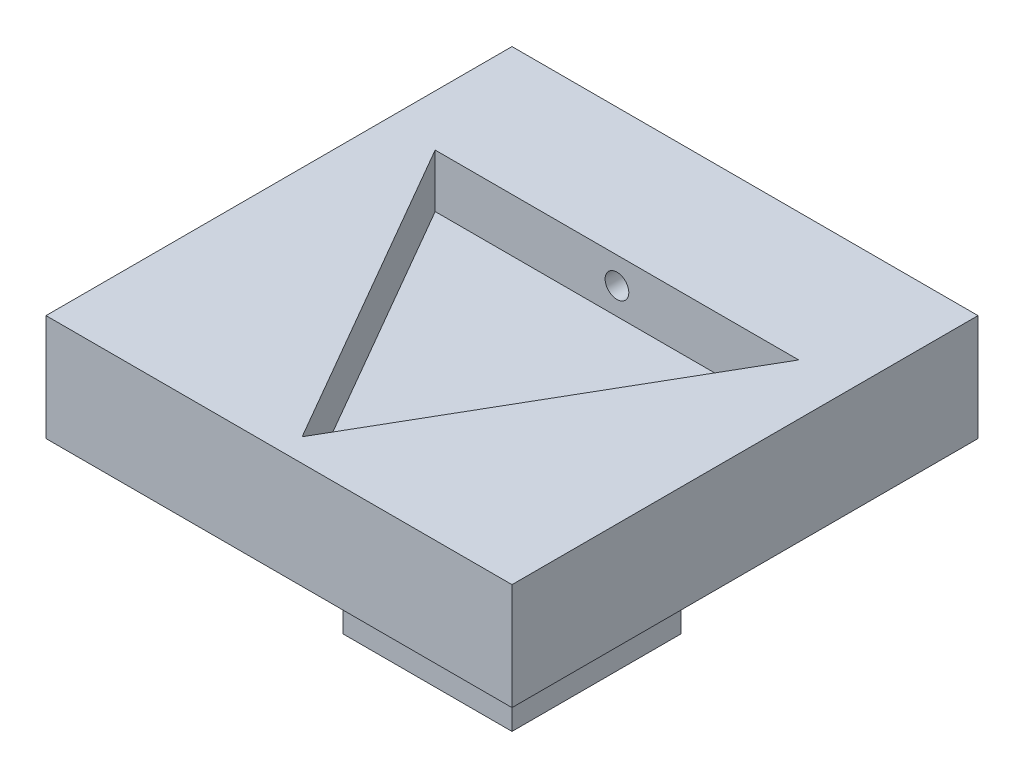
SolidWorks part; units mm, degrees
ref_plane "Front" through (0, 0, 0) normal (0, 0, 1) x (1, 0, 0)
ref_plane "Top" through (0, 0, 0) normal (0, 1, 0) x (1, 0, 0)
ref_plane "Right" through (0, 0, 0) normal (1, 0, 0) x (0, 0, -1)
sketch "Sketch1" plane through (0, 0, 0) normal (0, 1, 0) x (1, 0, 0)
  line L1 (-17.5, -17.5) -> (17.5, -17.5)
  line L2 (-17.5, -17.5) -> (-17.5, 17.5)
  line L3 (-17.5, 17.5) -> (17.5, 17.5)
  line L4 (17.5, -17.5) -> (17.5, 17.5)
  line L5 (-17.5, -17.5) -> (17.5, 17.5) construction
  line L6 (-17.5, 17.5) -> (17.5, -17.5) construction
  point P0 (0, 0)
  dimension "D1" = 35
  dimension "D2" = 35
extrude "Extrude1" add sketch "Sketch1" along normal blind 8
sketch "Sketch2" plane through (0, 8, 0) normal (0, 1, 0) x (1, 0, 0)
  line L0 (17.5, 17.5) -> (-17.5, 17.5) construction
  line L1 (0, -15.764) -> (13.652, 7.882)
  line L2 (13.652, 7.882) -> (-13.652, 7.882)
  line L3 (-13.652, 7.882) -> (0, -15.764)
  circle A0 centre (0, 0) radius 7.882 construction
  dimension "D1" = 23.646
  dimension "D2" = 17.5
extrude "Extrude2" cut sketch "Sketch2" against normal blind 4
sketch "Sketch3" plane through (0, 0, -17.5) normal (0, 0, -1) x (-1, 0, 0)
  line L0 (0, -15.1983) -> (0, 14.4979) construction
hole_wizard "#2-56 Tapped Hole1" positions "3DSketch1" profile "Sketch5" tap size "#2-56" standard "Ansi Inch" end condition up to next
sketch3d "3DSketch1"
  line L0 (0, -15.1983, -17.5) -> (0, 14.4979, -17.5) construction
  line L1 (17.5, 8, -17.5) -> (-17.5, 8, -17.5) construction
  point P0 (0, 6, -17.5)
  dimension "D1" = 2
sketch "Sketch5" plane through (0, 6, -17.5) normal (1, 0, 0) x (0, 1, 0)
  line L0 (0, 0) -> (0, 9.618)
  line L1 (0, 9.618) -> (0.889, 9.618)
  line L2 (0.889, 9.618) -> (0.889, 0)
  line L5 (0.889, 0) -> (0, 0)
  line L11 (0, -6.35) -> (0, 107.95) construction
  dimension "Thread Major Dia." = 1.778
  dimension "Thru Tap Drill Depth" = 9.618
sketch "Sketch6" plane through (0, 0, 0) normal (0, -1, 0) x (1, 0, 0)
  line L1 (-6.35, -6.35) -> (6.35, -6.35)
  line L2 (-6.35, -6.35) -> (-6.35, 6.35)
  line L3 (-6.35, 6.35) -> (6.35, 6.35)
  line L4 (6.35, -6.35) -> (6.35, 6.35)
  line L5 (-6.35, -6.35) -> (6.35, 6.35) construction
  line L6 (-6.35, 6.35) -> (6.35, -6.35) construction
  point P0 (0, 0)
  dimension "D1" = 12.7
  dimension "D2" = 12.7
extrude "Extrude3" add sketch "Sketch6" along normal blind 12.7
sketch "Sketch7" plane through (6.35, 0, 0) normal (1, 0, 0) x (0, 0, -1)
  line L0 (0, -16.8508) -> (0, 11.4455) construction
sketch "Sketch8" plane through (0, 0, 6.35) normal (0, 0, 1) x (1, 0, 0)
  line L0 (0, -17.0804) -> (0, 11.7392) construction
hole_wizard "1/4 (0.25) Diameter Hole1" positions "3DSketch2" profile "Sketch9" hole size "1/4" standard "Ansi Inch" end condition through all
sketch3d "3DSketch2"
  line L0 (0, -17.0804, 6.35) -> (0, 11.7392, 6.35) construction
  line L1 (6.35, -12.7, 6.35) -> (-6.35, -12.7, 6.35) construction
  point P0 (0, -6.35, 6.35)
  dimension "D1" = 6.35
sketch "Sketch9" plane through (0, -6.35, 6.35) normal (1, 0, 0) x (0, -1, 0)
  line L0 (0, 0) -> (0, 23.85)
  line L1 (0, 23.85) -> (3.175, 23.85)
  line L2 (3.175, 23.85) -> (3.175, 0)
  line L5 (3.175, 0) -> (0, 0)
  line L11 (0, -6.35) -> (0, 107.95) construction
  dimension "Thru Hole Dia." = 6.35
  dimension "Thru Hole Depth" = 23.85
hole_wizard "1/4 (0.25) Diameter Hole2" positions "3DSketch3" profile "Sketch10" hole size "1/4" standard "Ansi Inch" end condition through all
sketch3d "3DSketch3"
  line L0 (6.35, -16.8508, 0) -> (6.35, 11.4455, 0) construction
  line L1 (6.35, -12.7, -6.35) -> (6.35, -12.7, 6.35) construction
  point P0 (6.35, -6.35, 0)
  dimension "D1" = 6.35
sketch "Sketch10" plane through (6.35, -6.35, 0) normal (0, 1, 0) x (0, 0, -1)
  line L0 (0, 0) -> (0, 23.85)
  line L1 (0, 23.85) -> (3.175, 23.85)
  line L2 (3.175, 23.85) -> (3.175, 0)
  line L5 (3.175, 0) -> (0, 0)
  line L11 (0, -6.35) -> (0, 107.95) construction
  dimension "Thru Hole Dia." = 6.35
  dimension "Thru Hole Depth" = 23.85
hole_wizard "#2-56 Tapped Hole2" positions "3DSketch5" profile "Sketch14" tap size "#2-56" standard "Ansi Inch"
sketch3d "3DSketch5"
  line L0 (-6.35, -12.7, 6.35) -> (-6.35, -12.7, -6.35) construction
  line L2 (-6.35, -12.7, -6.35) -> (6.35, -12.7, -6.35) construction
  point P0 (0, 0, 0)
  point P5 (0, -12.7, 0)
  dimension "D1" = 6.35
  dimension "D2" = 6.35
sketch "Sketch14" plane through (0, -12.7, 0) normal (1, 0, 0) x (0, 0, -1)
  line L0 (0, 0) -> (0, 6.35)
  line L1 (0, 6.35) -> (0.889, 6.35)
  line L2 (0.889, 6.35) -> (0.889, 0)
  line L5 (0.889, 0) -> (0, 0)
  line L11 (0, -6.35) -> (0, 107.95) construction
  dimension "Thread Major Dia." = 1.778
  dimension "Thru Tap Drill Depth" = 6.35
